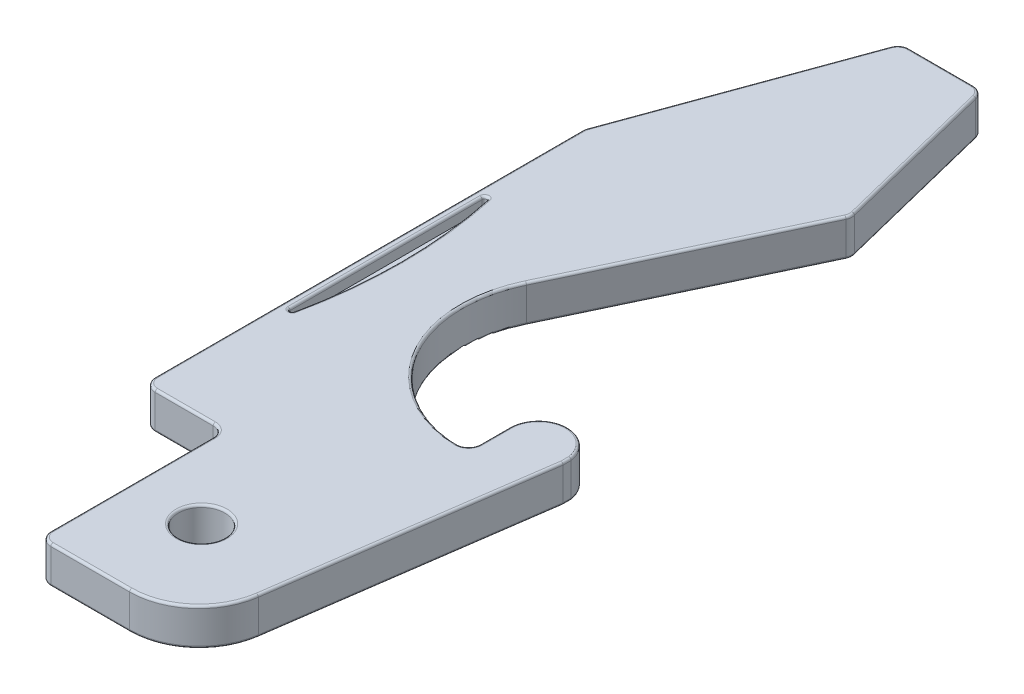
SolidWorks part; units mm, degrees
ref_plane "Front Plane" through (0, 0, 0) normal (0, 0, 1) x (1, 0, 0)
ref_plane "Top Plane" through (0, 0, 0) normal (0, 1, 0) x (1, 0, 0)
ref_plane "Right Plane" through (0, 0, 0) normal (1, 0, 0) x (0, 0, -1)
sketch "Sketch1" plane through (0, 0, 0) normal (0, 1, 0) x (1, 0, 0)
  line L0 (-21.6124, -49.4318) -> (-21.6124, -22.4318)
  line L1 (-21.6124, -49.4318) -> (-9.6124, -49.4318)
  line L2 (-21.6124, -49.4318) -> (-21.6124, -12.4318)
  line L3 (-21.6124, -12.4318) -> (-9.6124, -12.4318)
  line L4 (-9.6124, -49.4318) -> (-9.6124, -12.4318)
  line L5 (-21.6124, -22.4318) -> (-17.9744, -12.4318)
  line L6 (-17.9744, -12.4318) -> (-14.4744, -12.4318)
  line L7 (-14.4744, -12.4318) -> (-12.6124, -19.9318)
  line L8 (-12.6124, -19.9318) -> (-17.1154, -29.4318)
  line L9 (-12.0999, -36.9383) -> (-12.0999, -35.1818)
  line L10 (-9.6124, -35.3577) -> (-11.6124, -49.4318)
  line L11 (-11.6124, -49.4318) -> (-21.6124, -49.4318)
  arc A0 (-17.1154, -29.4318) -> (-12.0999, -36.9383) centre (-12.3624, -31.6848) ccw
  arc A1 (-12.0999, -35.1818) -> (-9.6124, -35.3577) centre (-10.8499, -35.1818) cw
  dimension "D10" = 1.25
  dimension "D11" = 5.26
  dimension "D1" = 37
  dimension "D2" = 12
  dimension "D3" = 10
  dimension "D4" = 3.5
  dimension "D5" = 3.638
  dimension "D6" = 10
  dimension "D7" = 7.5
  dimension "D8" = 9.5
  dimension "D9" = 22.75
  dimension "D12" = 9.25
  dimension "D13" = 9
extrude "Boss-Extrude1" add sketch "Sketch1" along normal blind 1.6 contours A1 L9 A0 L8 L7 L3 L5 L0 L1 L10 L4
fillet "Fillet1" radius 3 1 edges at (-11.6124, 0.8, 49.4318)
sketch "Sketch2" plane through (0, 0, 0) normal (0, 1, 0) x (1, 0, 0)
  line L0 (-21.6124, -49.4318) -> (-14.2162, -49.4318) construction
  line L1 (-21.6124, -49.4318) -> (-18.1124, -49.4318)
  line L2 (-21.6124, -49.4318) -> (-21.6124, -41.4318)
  line L3 (-21.6124, -41.4318) -> (-18.1124, -41.4318)
  line L4 (-18.1124, -49.4318) -> (-18.1124, -41.4318)
  circle A0 centre (-15.1124, -45.4318) radius 1
  dimension "D3" = 2
  dimension "D1" = 8
  dimension "D2" = 3.5
  dimension "D4" = 4
  dimension "D5" = 3
extrude "Cut-Extrude3" cut sketch "Sketch2" along normal through all
fillet "Fillet2" radius 0.5 8 edges at (-12.0999, 0.8, 36.9383) (-12.6124, 0.8, 19.9318) (-14.4744, 0.8, 12.4318) (-17.9744, 0.8, 12.4318) (-21.6124, 0.8, 22.4318) (-21.6124, 0.8, 41.4318) (-18.1124, 0.8, 41.4318) (-18.1124, 0.8, 49.4318)
fillet "Fillet4" radius 0.1 23 edges at (-15.1124, 0, 46.4318) (-14.5574, 0, 12.538) (-16.2448, 0, 12.4318) (-17.9111, 0, 12.5223) (-19.8382, 0, 17.555) (-21.6048, 0, 22.4332) (-21.6124, 0, 31.7259) (-21.4659, 0, 41.2854) (-19.8624, 0, 41.4318) (-18.2588, 0, 41.5783) (-18.1124, 0, 45.4318) (-17.9659, 0, 49.2854) (-15.9143, 0, 49.4318) (-12.2497, 0, 48.6975) (-10.4292, 0, 41.1058) (-9.6124, 0, 35.1818) (-10.9381, 0, 33.935) (-12.0999, 0, 35.8104) (-12.2553, 0, 36.8012) (-16.8763, 0, 34.3852) (-14.9021, 0, 24.7625) (-12.6431, 0, 19.9288) (-13.5178, 0, 16.285)
fillet "Fillet5" radius 0.1 23 edges at (-15.1124, 1.6, 46.4318) (-16.8763, 1.6, 34.3852) (-12.2553, 1.6, 36.8012) (-12.0999, 1.6, 35.8104) (-10.9381, 1.6, 33.935) (-9.6124, 1.6, 35.1818) (-10.4292, 1.6, 41.1058) (-12.2497, 1.6, 48.6975) (-15.9143, 1.6, 49.4318) (-17.9659, 1.6, 49.2854) (-18.1124, 1.6, 45.4318) (-18.2588, 1.6, 41.5783) (-19.8624, 1.6, 41.4318) (-21.4659, 1.6, 41.2854) (-21.6124, 1.6, 31.7259) (-21.6048, 1.6, 22.4332) (-19.8382, 1.6, 17.555) (-17.9111, 1.6, 12.5223) (-16.2448, 1.6, 12.4318) (-14.5574, 1.6, 12.538) (-13.5178, 1.6, 16.285) (-12.6431, 1.6, 19.9288) (-14.9021, 1.6, 24.7625)
sketch "Sketch4" plane through (0, 1.6, 0) normal (0, 1, 0) x (1, 0, 0)
  line L0 (-21.2624, -26.3318) -> (-21.2624, -36.3318)
  line L1 (-21.1124, -41.3318) -> (-18.6124, -41.3318) construction
  line L2 (-21.5124, -22.52) -> (-21.5124, -40.9318) construction
  arc A0 (-21.2624, -26.3318) -> (-21.2624, -36.3318) centre (-40.6273, -31.3318) cw
  dimension "D3" = 20
  dimension "D1" = 10
  dimension "D2" = 5
  dimension "D4" = 0.25
extrude "Cut-Extrude6" cut sketch "Sketch4" against normal blind 0.5
fillet "Fillet7" radius 0.1 1 edges at (-21.2624, 1.35, 36.3318)
fillet "Fillet8" radius 0.1 1 edges at (-21.2624, 1.35, 26.3318)
fillet "Fillet9" radius 0.1 4 edges at (-21.1728, 1.6, 35.5698) (-21.2624, 1.6, 31.3318) (-21.1728, 1.6, 27.0939) (-20.6273, 1.6, 31.3318)
